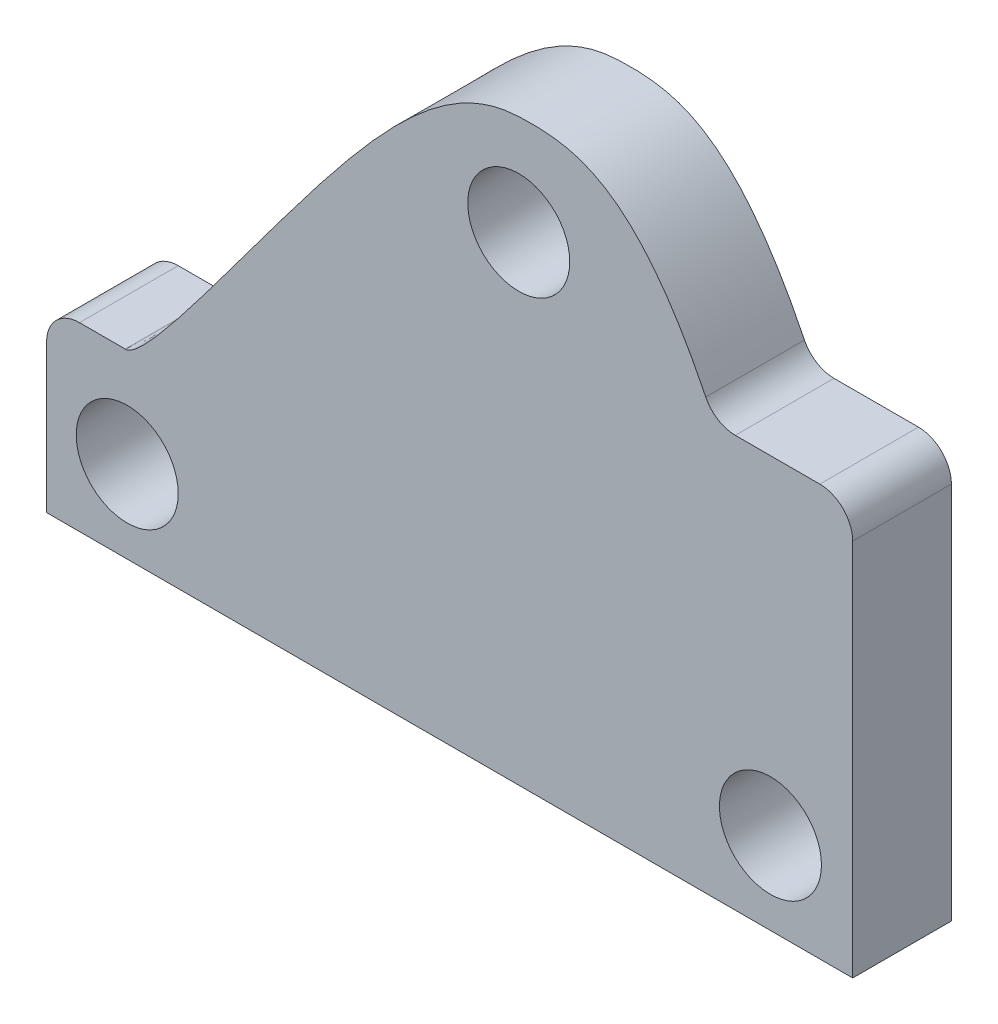
SolidWorks part; units mm, degrees
material "Default"
ref_plane "Front Plane" through (0, 0, 0) normal (0, 0, 1) x (1, 0, 0)
ref_plane "Top Plane" through (0, 0, 0) normal (0, 1, 0) x (1, 0, 0)
ref_plane "Right Plane" through (0, 0, 0) normal (1, 0, 0) x (0, 0, -1)
sketch "Sketch1" plane through (0, 0, 0) normal (0, 0, 1) x (1, 0, 0)
  line L0 (31.115, 6.858) -> (31.115, -22.352)
  line L1 (-31.115, -22.352) -> (31.115, -22.352)
  line L3 (-31.115, 22.352) -> (31.115, 22.352) construction
  line L7 (28.575, 9.398) -> (22.0522, 9.398)
  line L8 (-31.115, -22.352) -> (-31.115, -10.922)
  line L9 (-28.575, -8.382) -> (-25.0495, -8.382)
  circle A0 centre (5.334, 14.605) radius 3.937
  circle A1 centre (-24.892, -16.002) radius 3.937
  circle A2 centre (24.765, -16.002) radius 3.937
  arc A3 (19.7721, 10.8188) -> (22.0522, 9.398) centre (22.0522, 11.938) ccw
  arc A4 (-25.0088, -8.3823) -> (-25.0495, -8.382) centre (-25.0495, -10.922) ccw
  arc A5 (-28.575, -8.382) -> (-31.115, -10.922) centre (-28.575, -10.922) ccw
  arc A6 (31.115, 6.858) -> (28.575, 9.398) centre (28.575, 6.858) ccw
  spline S0 degree 3 poles (-25.0088, -8.3823) (-23.842, -8.401) (-18.103, -0.5571) (-6.2837, 15.2467) (0.0339, 22.0617) (9.0221, 22.5995) (14.6253, 21.3044) (19.7721, 10.8188) knots 0.000773 0.000773 0.000773 0.000773 0.263254 0.333795 0.664808 0.734461 0.988945 0.988945 0.988945 0.988945
  point P0 (0, 0)
  dimension "D7" = 6.35
  dimension "D8" = 36.957
  dimension "D9" = 7.874
  dimension "D3" = 2.54
  dimension "D5" = 2.54
  dimension "D16" = 2.54
  dimension "D17" = 2.54
  dimension "D2" = 25.781
  dimension "D4" = 6.223
  dimension "D6" = 13.97
  dimension "D10" = 62.23
  dimension "D11" = 6.35
  dimension "D12" = 22.352
  dimension "D13" = 6.35
  dimension "D14" = 31.75
  dimension "D15" = 31.115
extrude "Boss-Extrude1" add sketch "Sketch1" along normal mid plane 7.62
